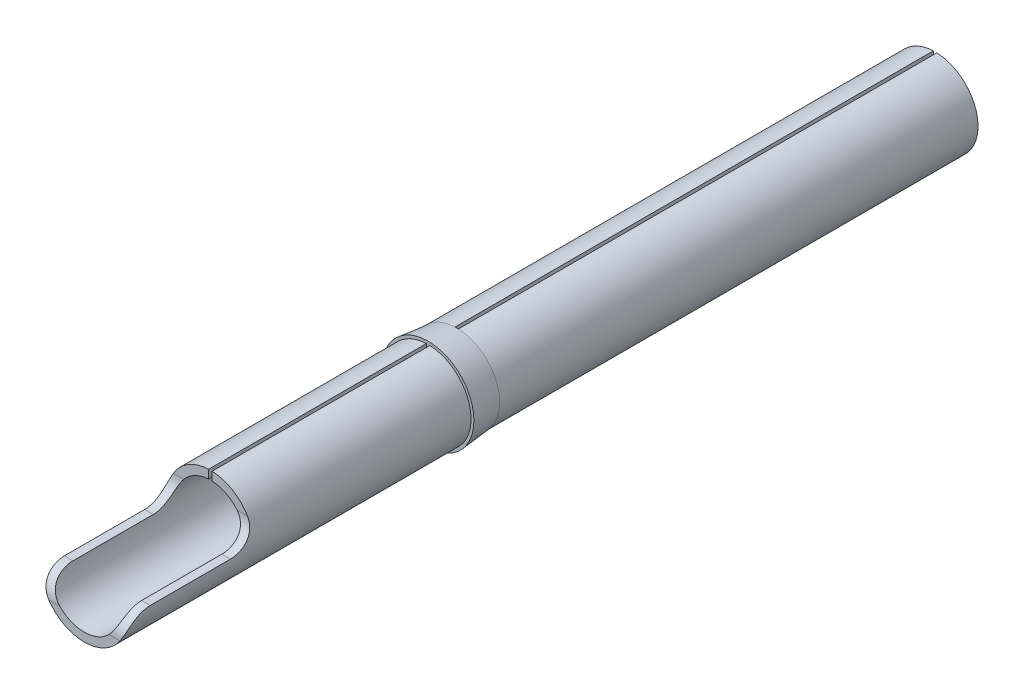
SolidWorks part; units mm, degrees
ref_plane "Front Plane" through (0, 0, 0) normal (0, 0, 1) x (1, 0, 0)
ref_plane "Top Plane" through (0, 0, 0) normal (0, 1, 0) x (1, 0, 0)
ref_plane "Right Plane" through (0, 0, 0) normal (1, 0, 0) x (0, 0, -1)
sketch "Sketch1" plane through (0, 0, 0) normal (0, 0, 1) x (1, 0, 0)
  circle A0 centre (0, 0) radius 0.75
  dimension "D1" = 1.5
extrude "Boss-Extrude1" add sketch "Sketch1" along normal blind 5.1
ref_plane "Plane1" through (0, 0, 0) normal (0, 0, 1) x (1, 0, 0)
sketch "Sketch8" plane through (0, 0, 5.1) normal (0, 0, 1) x (1, 0, 0)
  circle A1 centre (0, 0) radius 0.75
  circle A2 centre (0, 0) radius 0.75
  dimension "D1" = 0
extrude "Boss-Extrude2" add sketch "Sketch8" along normal blind 1.75
sketch "Sketch9" plane through (0, 0, 6.85) normal (0, 0, 1) x (1, 0, 0)
  circle A0 centre (0, 0) radius 0.75
  dimension "D1" = 1.5
extrude "Boss-Extrude3" add sketch "Sketch9" along normal blind 8
sketch "Sketch10" plane through (0, 0, 14.85) normal (0, 0, 1) x (1, 0, 0)
  line L0 (-0.6, 0) -> (-0.75, 0) construction
  circle A0 centre (0, 0) radius 0.6
  circle A1 centre (0, 0) radius 0.75 construction
  dimension "D1" = 0.15
extrude "Cut-Extrude7" cut sketch "Sketch10" against normal blind 5.65
sketch "Sketch11" plane through (0, 0, 0) normal (0, 0, -1) x (-1, 0, 0)
  circle A0 centre (0, 0) radius 0.5
  dimension "D1" = 1
extrude "Cut-Extrude8" cut sketch "Sketch11" against normal blind 6.5
sketch "Sketch12" plane through (0, 0, 14.85) normal (0, 0, 1) x (1, 0, 0)
  line L0 (0, 0.75) -> (0, -0.75) construction
  line L1 (-0.03, 0.7494) -> (-0.03, 0.5992)
  line L2 (0.03, 0.7494) -> (0.03, 0.5992)
  circle A0 centre (0, 0) radius 0.75 construction
  arc A1 (0.03, 0.7494) -> (-0.03, 0.7494) centre (0, 0) ccw
  circle A2 centre (0, 0) radius 0.6 construction
  arc A3 (0.03, 0.5992) -> (-0.03, 0.5992) centre (0, 0) ccw
  dimension "D1" = 0.03
extrude "Cut-Extrude9" cut sketch "Sketch12" against normal up to surface (14.85 mm away) up to face at (-0.5, 0, 0)
sketch "Sketch14" plane through (0, 0, 0) normal (0, 0, -1) x (-1, 0, 0)
  line L0 (-0.03, 0.7494) -> (-0.03, 0.4991)
  line L1 (0.03, 0.7494) -> (0.03, 0.4991)
  circle A0 centre (0, 0) radius 0.5 construction
  arc A1 (0.03, 0.7494) -> (-0.03, 0.7494) centre (0, 0) ccw
  circle A2 centre (0, 0) radius 0.5
  arc A3 (0.03, 0.4991) -> (-0.03, 0.4991) centre (0, 0) ccw
  dimension "D1" = 0
extrude "Cut-Extrude10" cut sketch "Sketch14" against normal up to surface (6.5 mm away) up to face at (-0.5, 0, 6.5)
fillet "Fillet2" radius 0.15 1 edges at (0, -0.5, 0)
sketch "Sketch15" plane through (0, 0, 14.85) normal (0, 0, 1) x (1, 0, 0)
  line L0 (-0.7497, -0.02) -> (-0.5997, -0.02)
  line L1 (-0.03, 0.7494) -> (-0.03, 0.5992) construction
  line L2 (-0.03, 0.7494) -> (-0.03, 0.5992)
  line L3 (0.03, 0.5992) -> (0.03, 0.7494) construction
  line L4 (0.03, 0.5992) -> (0.03, 0.7494)
  line L5 (0.5997, -0.02) -> (0.7497, -0.02)
  arc A0 (-0.03, 0.7494) -> (-0.7497, -0.02) centre (0, 0) ccw
  arc A1 (-0.03, 0.5992) -> (0.03, 0.5992) centre (0, 0) ccw construction
  arc A2 (-0.03, 0.5992) -> (-0.5997, -0.02) centre (0, 0) ccw
  arc A3 (0.5997, -0.02) -> (0.03, 0.5992) centre (0, 0) ccw
  arc A4 (0.7497, -0.02) -> (0.03, 0.7494) centre (0, 0) ccw
  point P6 (0, -0.75)
  dimension "D1" = 0.73
extrude "Cut-Extrude11" cut sketch "Sketch15" against normal blind 2.2
fillet "Fillet3" radius 0.4 4 edges at (-0.6747, -0.02, 14.85) (0.6747, -0.02, 14.85) (-0.6747, -0.02, 12.65) (0.6747, -0.02, 12.65)
ref_plane "Plane2" through (0, 0, 8.85) normal (0, 0, 1) x (1, 0, 0)
sketch "Sketch16" plane through (0, 0, 8.85) normal (0, 0, 1) x (1, 0, 0)
  circle A0 centre (0, 0) radius 0.8
  dimension "D1" = 1.6
ref_plane "Plane3" through (0, 0, 8.35) normal (0, 0, 1) x (1, 0, 0)
sketch "Sketch17" plane through (0, 0, 8.35) normal (0, 0, 1) x (1, 0, 0)
  circle A0 centre (0, 0) radius 0.75
  dimension "D1" = 1.5
loft "Loft1" add profiles "Sketch17", "Sketch16"
ref_plane "Plane4" through (0, 0, -0.4) normal (0, 0, -1) x (-1, 0, 0)
